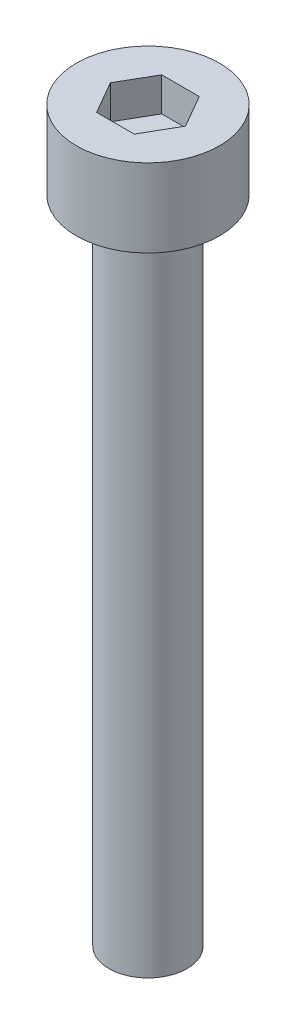
SolidWorks part; units mm, degrees
material "AISI 304"
ref_plane "前视基准面" through (0, 0, 0) normal (0, 0, 1) x (1, 0, 0)
ref_plane "上视基准面" through (0, 0, 0) normal (0, 1, 0) x (1, 0, 0)
ref_plane "右视基准面" through (0, 0, 0) normal (1, 0, 0) x (0, 0, -1)
sketch "草图1" plane through (0, 0, 0) normal (0, 1, 0) x (1, 0, 0)
  circle A0 centre (0, 0) radius 2.75
  dimension "D1" = 5.5
extrude "杯头" add sketch "草图1" along normal blind 3
sketch "草图2" plane through (0, 3, 0) normal (0, 1, 0) x (1, 0, 0)
  line L1 (1.4434, 0) -> (0.7217, 1.25)
  line L2 (0.7217, 1.25) -> (-0.7217, 1.25)
  line L3 (-0.7217, 1.25) -> (-1.4434, 0)
  line L4 (-1.4434, 0) -> (-0.7217, -1.25)
  line L5 (-0.7217, -1.25) -> (0.7217, -1.25)
  line L6 (0.7217, -1.25) -> (1.4434, 0)
  circle A0 centre (0, 0) radius 1.25 construction
  dimension "D1" = 2.5
extrude "内六角口" cut sketch "草图2" against normal blind 1.3
sketch "草图3" plane through (0, 0, 0) normal (0, -1, 0) x (1, 0, 0)
  circle A0 centre (0, 0) radius 1.5
  dimension "D1" = 3
extrude "螺纹长" add sketch "草图3" along normal blind 25
